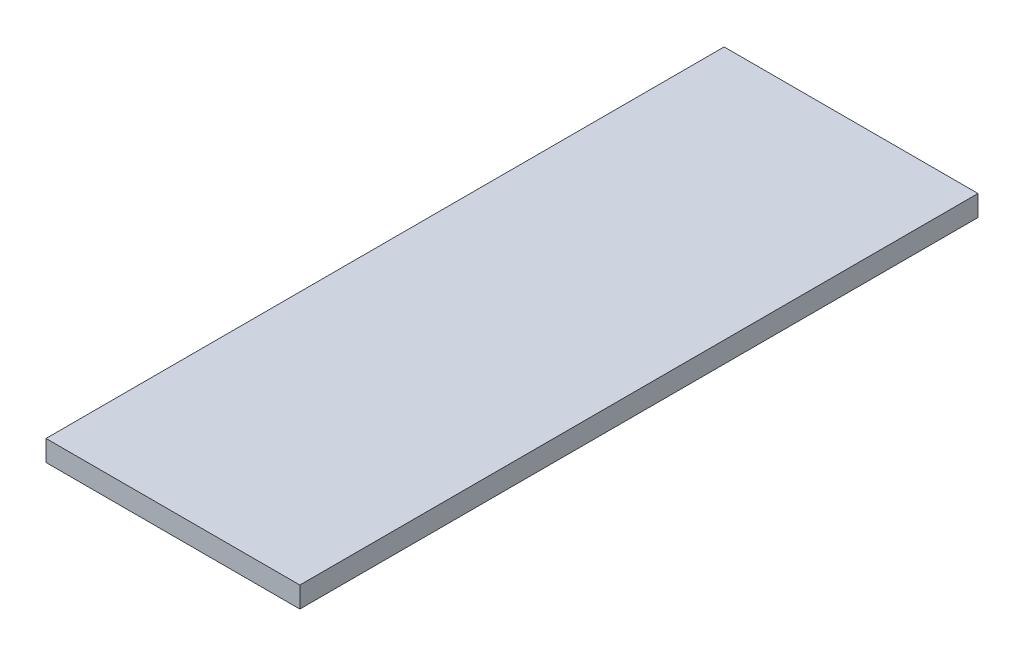
SolidWorks part; units mm, degrees
material "Silicon Rubber"
ref_plane "Front" through (0, 0, 0) normal (0, 0, 1) x (1, 0, 0)
ref_plane "Top" through (0, 0, 0) normal (0, 1, 0) x (1, 0, 0)
ref_plane "Right" through (0, 0, 0) normal (1, 0, 0) x (0, 0, -1)
sketch "Sketch1" plane through (0, 0, 0) normal (0, 1, 0) x (1, 0, 0)
  line L0 (21.23, -67.5) -> (-21.23, -67.5) construction
  line L1 (-19.325, -64.325) -> (19.325, -64.325)
  line L2 (-19.325, -64.325) -> (-19.325, 64.325)
  line L3 (-19.325, 64.325) -> (19.325, 64.325)
  line L4 (19.325, -64.325) -> (19.325, 64.325)
  line L5 (-19.325, -64.325) -> (19.325, 64.325) construction
  line L6 (-19.325, 64.325) -> (19.325, -64.325) construction
  line L7 (22.5, -70.675) -> (22.5, 70.4954) construction
  point P0 (0, 0)
  dimension "D1" = 3.175
  dimension "D2" = 3.175
extrude "Boss-Extrude1" add sketch "Sketch1" along normal blind 3.175
sketch "Sketch5" plane through (0, 3.175, 0) normal (0, 1, 0) x (1, 0, 0)
  line L0 (19.325, -64.325) -> (19.325, 64.325) construction
  line L1 (-19.325, 64.325) -> (19.325, 64.325)
  line L2 (-19.325, 64.325) -> (-19.325, 38.925)
  line L3 (-19.325, 38.925) -> (19.325, 38.925)
  line L4 (19.325, 64.325) -> (19.325, 38.925)
  dimension "D1" = 25.4
extrude "Cut-Extrude3" cut sketch "Sketch5" against normal through all
